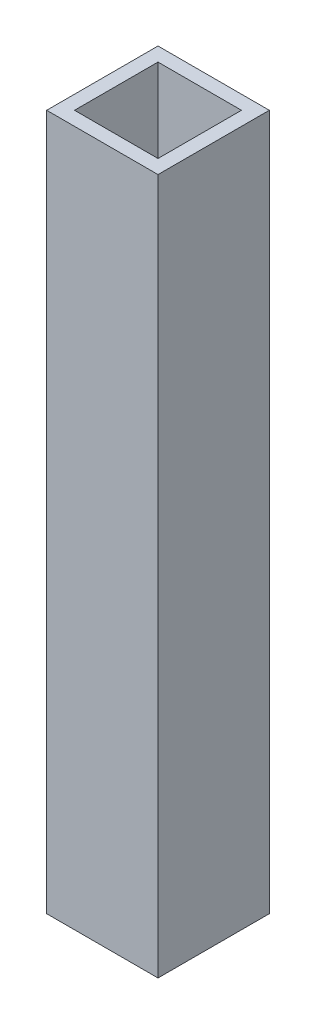
SolidWorks part; units mm, degrees
ref_plane "Front Plane" through (0, 0, 0) normal (0, 0, 1) x (1, 0, 0)
ref_plane "Top Plane" through (0, 0, 0) normal (0, 1, 0) x (1, 0, 0)
ref_plane "Right Plane" through (0, 0, 0) normal (1, 0, 0) x (0, 0, -1)
sketch "Sketch1" plane through (0, 0, 0) normal (0, 1, 0) x (1, 0, 0)
  line L0 (-5, -5) -> (-5, 35)
  line L1 (0, 0) -> (30, 0)
  line L2 (0, 0) -> (0, 30)
  line L3 (0, 30) -> (30, 30)
  line L4 (30, 0) -> (30, 30)
  line L5 (-5, 35) -> (35, 35)
  line L6 (35, -5) -> (35, 35)
  line L7 (-5, -5) -> (35, -5)
  dimension "D1" = 30
  dimension "D2" = 30
  dimension "D3" = 5
extrude "Boss-Extrude1" add sketch "Sketch1" along normal blind 250
